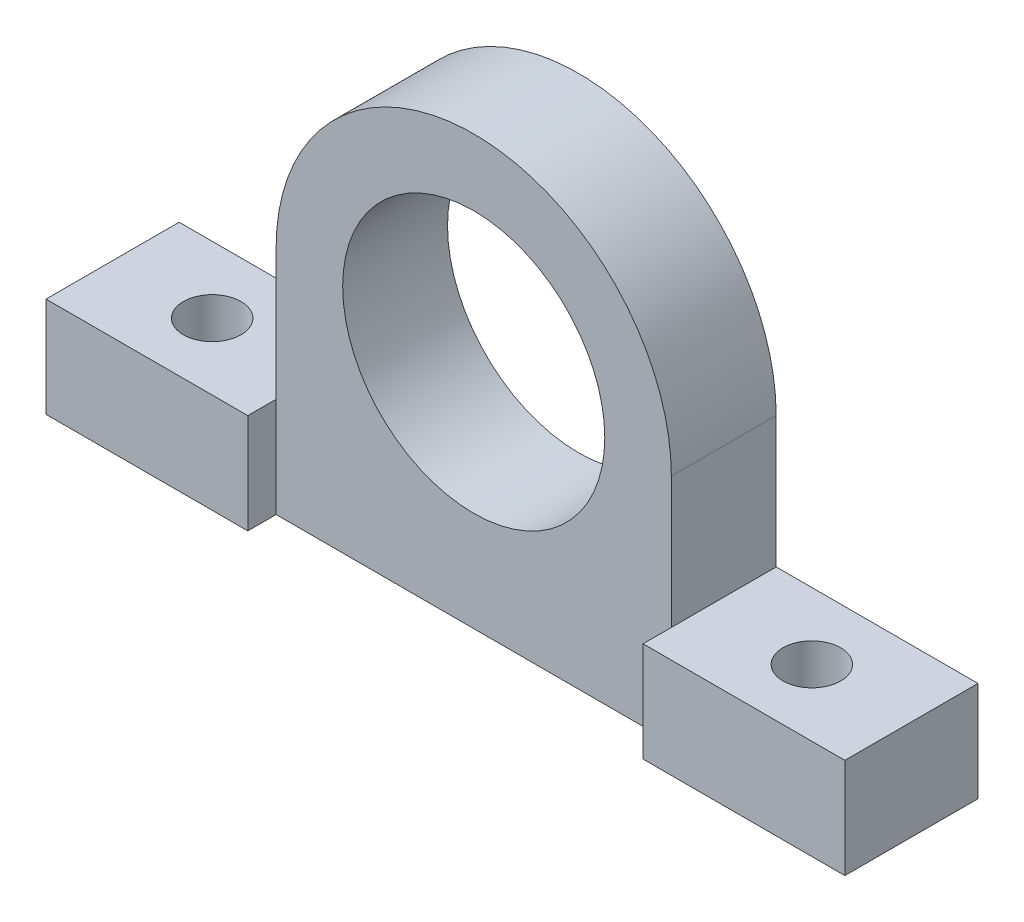
SolidWorks part; units mm, degrees
ref_plane "Front Plane" through (0, 0, 0) normal (0, 0, 1) x (1, 0, 0)
ref_plane "Top Plane" through (0, 0, 0) normal (0, 1, 0) x (1, 0, 0)
ref_plane "Right Plane" through (0, 0, 0) normal (1, 0, 0) x (0, 0, -1)
sketch "Sketch1" plane through (0, 0, 0) normal (0, 0, 1) x (1, 0, 0)
  line L5 (-76.2, -44.05) -> (-76.2, -25)
  line L6 (-76.2, -25) -> (76.2, -25)
  line L7 (-76.2, -44.05) -> (76.2, -44.05)
  line L8 (37.7, -25) -> (37.7, 0)
  line L9 (-37.7, -25) -> (-37.7, 0)
  line L10 (76.2, -44.05) -> (76.2, -25)
  arc A2 (37.7, 0) -> (-37.7, 0) centre (0, 0) ccw
  circle A3 centre (0, 0) radius 25
extrude "Boss-Extrude1" add sketch "Sketch1" along normal blind 20 contours L6 A3 L8 A2 L9 | L7 L10 L6 L5
sketch "Sketch2" plane through (0, 0, 20) normal (0, 0, 1) x (1, 0, 0)
  line L0 (-76.2, -25) -> (-37.7, -25) construction
  line L1 (-76.2, -44.05) -> (-76.2, -25) construction
  line L2 (-76.2, -44.05) -> (76.2, -44.05) construction
  line L3 (37.7, -25) -> (76.2, -25) construction
  line L4 (76.2, -44.05) -> (76.2, -25) construction
  line L5 (-76.2, -25) -> (-37.7, -25)
  line L6 (-76.2, -44.05) -> (-76.2, -25)
  line L7 (-76.2, -44.05) -> (76.2, -44.05)
  line L8 (37.7, -25) -> (76.2, -25)
  line L9 (76.2, -44.05) -> (76.2, -25)
  line L10 (-37.7, -25) -> (-37.7, -44.05)
  line L11 (37.7, -25) -> (37.7, -44.05)
  line M3 (-37.7, -25) -> (-76.2, -25)
  line M4 (-76.2, -25) -> (-76.2, -44.05)
  line M5 (-76.2, -44.05) -> (76.2, -44.05)
  line M6 (76.2, -44.05) -> (76.2, -25)
  line M7 (76.2, -25) -> (37.7, -25)
extrude "Boss-Extrude2" add sketch "Sketch2" along normal blind 5.4 contours L10 M3 M4 M5 | L11 M7 M5 M6
sketch "Sketch3" plane through (0, -25, 0) normal (0, 1, 0) x (1, 0, 0)
  line L0 (-76.2, -12.7) -> (76.2, -12.7) construction
  line L1 (-76.2, -25.4) -> (-76.2, 0) construction
  line L2 (76.2, -25.4) -> (76.2, 0) construction
  point P6 (-57.2, -12.7)
  point P7 (57.2, -12.7)
  dimension "D1" = 19
  dimension "D2" = 19
hole_wizard "M10 Clearance Hole1" positions "Sketch5" profile "Sketch4" hole size "M10" standard "ANSI Metric" end condition through all
sketch "Sketch5" plane through (0, -25, 0) normal (0, 1, 0) x (1, 0, 0)
  point P0 (-57.2, -12.7)
  point P3 (57.2, -12.7)
sketch "Sketch4" plane through (-57.2, -25, 12.7) normal (1, 0, 0) x (0, 0, 1)
  line L0 (0, 0) -> (0, 19.0501)
  line L1 (0, 19.0501) -> (5.5, 19.0501)
  line L2 (5.5, 19.0501) -> (5.5, 0)
  line L5 (5.5, 0) -> (0, 0)
  line L11 (0, -6.35) -> (0, 107.95) construction
  dimension "Thru Hole Dia." = 11
  dimension "Thru Hole Depth" = 19.0501
